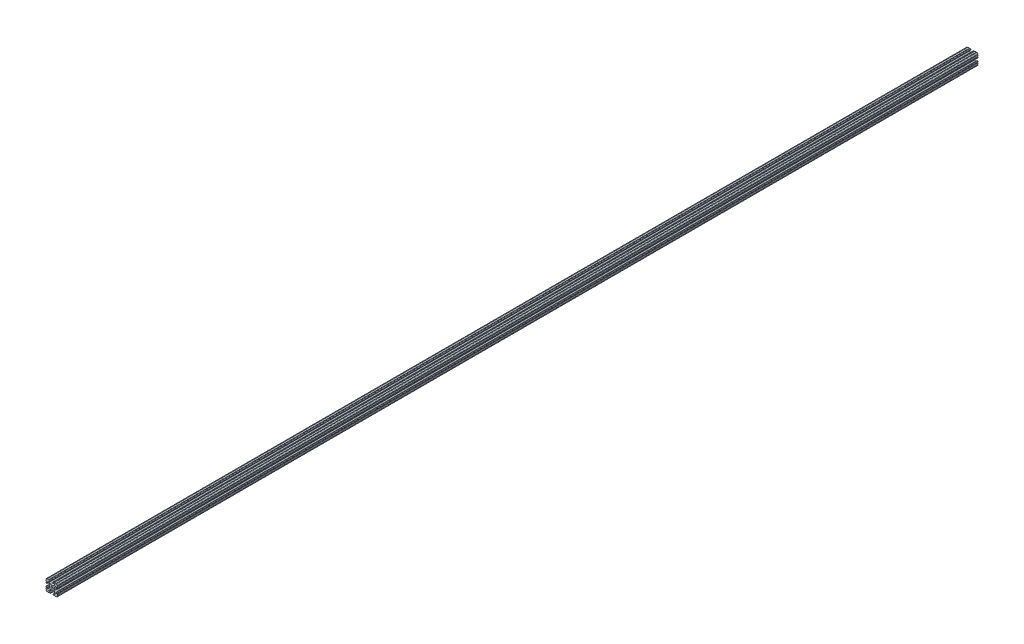
SolidWorks part; units mm, degrees
ref_plane "Front Plane" through (0, 0, 0) normal (0, 0, 1) x (1, 0, 0)
ref_plane "Top Plane" through (0, 0, 0) normal (0, 1, 0) x (1, 0, 0)
ref_plane "Right Plane" through (0, 0, 0) normal (1, 0, 0) x (0, 0, -1)
sketch "Sketch2" plane through (0, 0, 0) normal (0, 0, 1) x (1, 0, 0)
  line L0 (0, 19.05) -> (0, -19.05) construction
  line L1 (-19.05, 0) -> (19.05, 0) construction
  line L2 (4.064, -19.05) -> (19.05, -19.05)
  line L3 (19.05, -19.05) -> (19.05, -4.064)
  line L4 (4.064, -19.05) -> (4.064, -14.986)
  line L5 (4.064, -14.986) -> (12.1123, -14.986)
  line L6 (12.1123, -14.986) -> (4.1113, -6.985)
  line L7 (0, 0) -> (19.05, -19.05) construction
  line L8 (19.05, -4.064) -> (14.986, -4.064)
  line L9 (14.986, -4.064) -> (14.986, -12.1123)
  line L10 (14.986, -12.1123) -> (6.985, -4.1113)
  circle A0 centre (0, 0) radius 3.3274
  arc A1 (8.9963, -14.986) -> (9.909, -12.7826) centre (8.9963, -13.6953) ccw construction
  point P8 (0, -6.985)
  dimension "Center Hole Diameter" = 6.6548
  dimension "Rail Height" = 38.1
  dimension "Rail Width" = 38.1
  dimension "T-Slot Width" = 8.128
  dimension "Slot Inner Width" = 20.574
  dimension "Thickness" = 4.064
  dimension "Slot Depth" = 8.001
  dimension "D1" = 4.064
sketch "Sketch3" plane through (0, 0, 0) normal (1, 0, 0) x (0, 0, -1)
  line L0 (-1524, -19.05) -> (1524, -19.05) construction
  line L1 (-1498.6, 0) -> (1498.6, 0) construction
  dimension "Length" = 3048
  dimension "D1" = 25.4
sketch "Sketch4" plane through (0, 0, 0) normal (0, 0, 1) x (1, 0, 0)
  line L0 (5.7912, -19.05) -> (14.3002, -19.05)
  line L1 (4.064, -19.05) -> (19.05, -19.05) construction
  line L2 (4.064, -19.05) -> (4.064, -14.986) construction
  line L3 (4.064, -14.986) -> (12.1123, -14.986) construction
  line L4 (4.064, -16.7132) -> (4.064, -17.3228)
  line L5 (5.7912, -14.986) -> (8.9963, -14.986)
  line L6 (0, -6.985) -> (2.833, -6.985)
  line L7 (12.1123, -14.986) -> (4.1113, -6.985) construction
  line L8 (5.0152, -7.8889) -> (9.909, -12.7826)
  line L9 (19.05, -19.05) -> (19.05, -4.064) construction
  line L10 (14.986, -12.1123) -> (6.985, -4.1113) construction
  line L11 (14.986, -4.064) -> (14.986, -12.1123) construction
  line L12 (14.986, -8.9963) -> (14.986, -5.7912)
  line L13 (19.05, -4.064) -> (14.986, -4.064) construction
  line L14 (16.7132, -4.064) -> (17.3228, -4.064)
  line L15 (19.05, -5.7912) -> (19.05, -14.3002)
  line L16 (12.7826, -9.909) -> (7.8889, -5.0152)
  line L17 (6.985, 0) -> (6.985, -2.833)
  line L18 (-19.05, 0) -> (19.05, 0) construction
  line L19 (0, -6.985) -> (0, -3.3274)
  line L20 (0, 19.05) -> (0, -19.05) construction
  line L21 (6.985, 0) -> (3.3274, 0)
  arc A0 (4.064, -17.3228) -> (5.7912, -19.05) centre (5.7912, -17.3228) ccw
  arc A2 (4.064, -16.7132) -> (5.7912, -14.986) centre (5.7912, -16.7132) cw
  arc A3 (8.9963, -14.986) -> (9.909, -12.7826) centre (8.9963, -13.6953) ccw
  arc A4 (2.833, -6.985) -> (5.0152, -7.8889) centre (2.833, -10.0711) cw
  arc A5 (14.3002, -19.05) -> (19.05, -14.3002) centre (14.3002, -14.3002) ccw
  arc A6 (12.7826, -9.909) -> (14.986, -8.9963) centre (13.6953, -8.9963) ccw
  arc A7 (14.986, -5.7912) -> (16.7132, -4.064) centre (16.7132, -5.7912) cw
  arc A8 (17.3228, -4.064) -> (19.05, -5.7912) centre (17.3228, -5.7912) cw
  arc A9 (7.8889, -5.0152) -> (6.985, -2.833) centre (10.0711, -2.833) cw
  circle A10 centre (0, 0) radius 3.3274 construction
  arc A11 (0, -3.3274) -> (3.3274, 0) centre (0, 0) ccw
  dimension "D1" = 4.7498
  dimension "D2" = 3.0861
  dimension "D3" = 1.7272
extrude "Boss-Extrude1" add sketch "Sketch4" along normal mid plane 3048
sketch "Sketch5" plane through (0, 0, 0) normal (0, 0, 1) x (1, 0, 0)
  line L0 (4.064, -19.05) -> (19.05, -19.05) construction
  line L1 (5.7912, -14.986) -> (8.9963, -14.986) construction
  line L3 (0, 0) -> (19.05, -19.05) construction
  line L4 (8.9963, -14.986) -> (8.9963, -19.05) construction
  line L5 (12.1123, -14.986) -> (4.1113, -6.985) construction
  circle A0 centre (14.7395, -19.05) radius 1.016
  circle A1 centre (7.9803, -19.05) radius 1.016
  circle A2 centre (19.05, -14.7395) radius 1.016
  circle A3 centre (19.05, -7.9803) radius 1.016
  point P10 (7.3938, -14.986)
  point P12 (13.6953, -8.9963)
  dimension "D1" = 2.032
extrude "Cut-Extrude1" cut sketch "Sketch5" against normal through all both and the other way through all
mirror "Mirror1" about plane through (0, 0, 0) normal (1, 0, 0) of bodies 137 134
mirror "Mirror2" about plane through (0, 0, 0) normal (0, 1, 0) of bodies 135
equation "\"D1@Boss-Extrude1\"=\"Length@Sketch3\""
equation "\"D1@Sketch2\"=\"Thickness@Sketch2\""
equation "\"D2@Sketch4\"=\"Slot Inner Width@Sketch2\"*0.15"
equation "\"D1@Sketch4\"=\"D3@Sketch4\"*2.75"
equation "\"D3@Sketch4\"=\"Thickness@Sketch2\"*0.425"
equation "\"D1@Sketch5\"=\"Thickness@Sketch2\"*0.5"
